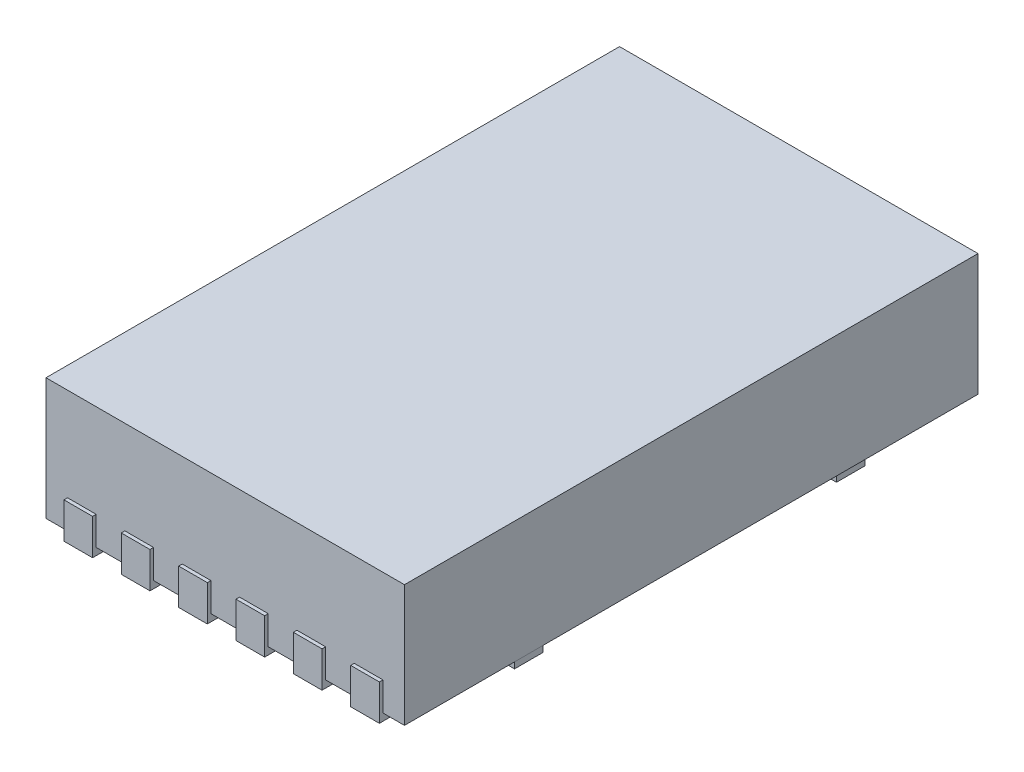
SolidWorks part; units mm, degrees
ref_plane "Front Plane" through (0, 0, 0) normal (0, 0, 1) x (1, 0, 0)
ref_plane "Top Plane" through (0, 0, 0) normal (0, 1, 0) x (1, 0, 0)
ref_plane "Right Plane" through (0, 0, 0) normal (1, 0, 0) x (0, 0, -1)
sketch "Sketch1" plane through (0, 0, 0) normal (0, 1, 0) x (1, 0, 0)
  line L1 (0, 0) -> (2.5, 0)
  line L2 (0, 0) -> (0, 4)
  line L3 (0, 4) -> (2.5, 4)
  line L4 (2.5, 0) -> (2.5, 4)
  dimension "D1" = 2.5
  dimension "D2" = 4
extrude "Boss-Extrude1" add sketch "Sketch1" along normal blind 0.85
sketch "Sketch2" plane through (0, 0, 0) normal (0, -1, 0) x (1, 0, 0)
  line L0 (1.75, 0.025) -> (1.75, -0.3321)
  line L2 (1.95, 0.025) -> (1.75, 0.025)
  line L3 (1.35, 0.025) -> (1.35, -0.3321)
  line L4 (1.55, 0.025) -> (1.55, -0.3321)
  line L5 (1.95, 0.025) -> (1.95, -0.3321)
  line L6 (1.55, 0.025) -> (1.35, 0.025)
  line L7 (2.15, 0.025) -> (2.15, -0.3321)
  line L8 (2.35, 0.025) -> (2.15, 0.025)
  line L9 (2.35, 0.025) -> (2.35, -0.3321)
  line L10 (1.35, 0.025) -> (1.35, -0.3321)
  line L11 (1.55, 0.025) -> (1.35, 0.025)
  line L12 (1.55, 0.025) -> (1.55, -0.3321)
  line L13 (1.75, 0.025) -> (1.75, -0.3321)
  line L14 (1.95, 0.025) -> (1.75, 0.025)
  line L15 (1.95, 0.025) -> (1.95, -0.3321)
  line L16 (0.95, 0.025) -> (0.95, -0.3321)
  line L17 (1.15, 0.025) -> (0.95, 0.025)
  line L18 (1.15, 0.025) -> (1.15, -0.3321)
  line L19 (1.35, 0.025) -> (1.35, -0.3321)
  line L20 (1.55, 0.025) -> (1.35, 0.025)
  line L21 (1.55, 0.025) -> (1.55, -0.3321)
  line L22 (0.55, 0.025) -> (0.55, -0.3321)
  line L23 (0.75, 0.025) -> (0.55, 0.025)
  line L24 (0.75, 0.025) -> (0.75, -0.3321)
  line L25 (0.95, 0.025) -> (0.95, -0.3321)
  line L26 (1.15, 0.025) -> (0.95, 0.025)
  line L27 (1.15, 0.025) -> (1.15, -0.3321)
  line L28 (0.95, 0.025) -> (0.95, -0.3321)
  line L29 (1.15, 0.025) -> (0.95, 0.025)
  line L30 (1.15, 0.025) -> (1.15, -0.3321)
  line L31 (0.55, 0.025) -> (0.55, -0.3321)
  line L32 (0.75, 0.025) -> (0.55, 0.025)
  line L33 (0.75, 0.025) -> (0.75, -0.3321)
  line L34 (0.15, 0.025) -> (0.15, -0.3321)
  line L35 (0.35, 0.025) -> (0.15, 0.025)
  line L36 (0.35, 0.025) -> (0.35, -0.3321)
  arc A0 (1.35, -0.3321) -> (1.55, -0.3321) centre (1.45, -0.2924) ccw
  arc A1 (1.75, -0.3321) -> (1.95, -0.3321) centre (1.85, -0.2924) ccw
  arc A2 (2.15, -0.3321) -> (2.35, -0.3321) centre (2.25, -0.2924) ccw
  arc A3 (1.35, -0.3321) -> (1.55, -0.3321) centre (1.45, -0.2924) ccw
  arc A4 (1.75, -0.3321) -> (1.95, -0.3321) centre (1.85, -0.2924) ccw
  arc A5 (0.95, -0.3321) -> (1.15, -0.3321) centre (1.05, -0.2924) ccw
  arc A6 (1.35, -0.3321) -> (1.55, -0.3321) centre (1.45, -0.2924) ccw
  arc A7 (0.55, -0.3321) -> (0.75, -0.3321) centre (0.65, -0.2924) ccw
  arc A8 (0.95, -0.3321) -> (1.15, -0.3321) centre (1.05, -0.2924) ccw
  arc A9 (0.95, -0.3321) -> (1.15, -0.3321) centre (1.05, -0.2924) ccw
  arc A10 (0.55, -0.3321) -> (0.75, -0.3321) centre (0.65, -0.2924) ccw
  arc A11 (0.15, -0.3321) -> (0.35, -0.3321) centre (0.25, -0.2924) ccw
  line M8 (2.5, 0) -> (0, 0)
  dimension "D1" = 3
  dimension "D2" = 4
extrude "Boss-Extrude2" add sketch "Sketch2" along normal blind 0.25 from offset 0.2 contours L34 A11 L36 M8 | L22 A7 L24 M8 | L16 A5 L18 M8 | L3 A0 L4 M8 | L4 L6 L3 M8 | L0 A1 L5 M8 | L7 A2 L9 M8 offset against normal yes
ref_plane "Plane1" through (0, 0, -2) normal (0, 0, 1) x (1, 0, 0)
mirror "Mirror1" about plane through (0, 0, -2) normal (0, 0, 1) of "Boss-Extrude2"
sketch "Sketch4" plane through (0, 0, 0) normal (0, -1, 0) x (1, 0, 0)
  line L0 (0, -2) -> (1.25, -2)
  line L1 (0, -4) -> (0, 0) construction
  line L2 (0.495, -2) -> (-0.495, -2) construction
  line L3 (2.225, -3.025) -> (2.4882, -3.025)
  line L4 (0.0093, -0.975) -> (0.275, -0.975)
  line L5 (0.0093, -0.775) -> (1.25, -0.775)
  line L6 (0.0093, -3.025) -> (0.275, -3.025)
  line L8 (0.0093, -3.225) -> (1.25, -3.225)
  line L9 (1.25, -3.225) -> (2.4882, -3.225)
  line L11 (1.25, -0.775) -> (2.4925, -0.775)
  line L12 (2.4925, -0.775) -> (2.4925, -0.975)
  line L13 (2.225, -3.025) -> (2.225, -0.975)
  line L14 (2.225, -0.975) -> (2.4925, -0.975)
  line L16 (0.0093, -0.775) -> (0.0093, -0.975)
  line L17 (0.275, -3.025) -> (0.275, -0.975)
  line L18 (2.4882, -3.025) -> (2.4882, -3.225)
  line L19 (0.0093, -3.225) -> (0.0093, -3.025)
extrude "Boss-Extrude3" add sketch "Sketch4" along normal blind 0.05
